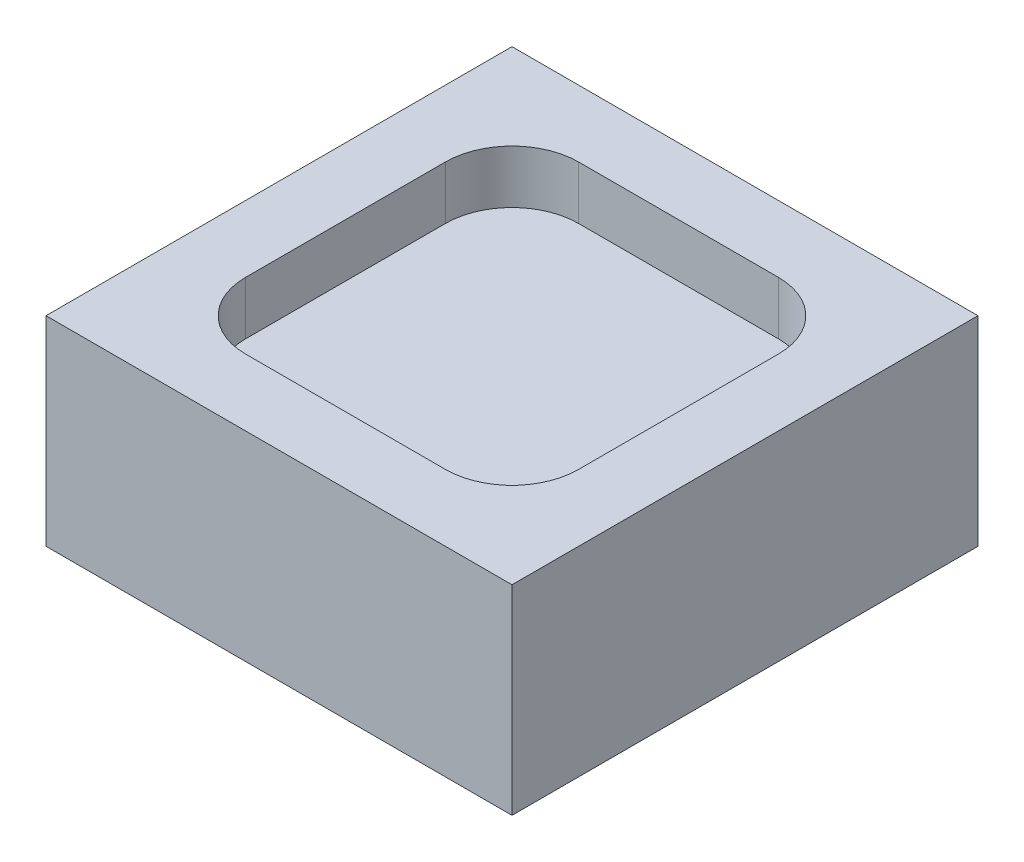
SolidWorks part; units mm, degrees
ref_plane "Front Plane" through (0, 0, 0) normal (0, 0, 1) x (1, 0, 0)
ref_plane "Top Plane" through (0, 0, 0) normal (0, 1, 0) x (1, 0, 0)
ref_plane "Right Plane" through (0, 0, 0) normal (1, 0, 0) x (0, 0, -1)
sketch "Sketch1" plane through (0, 0, 0) normal (0, 1, 0) x (1, 0, 0)
  line L1 (-3.5, 3.5) -> (3.5, 3.5)
  line L2 (-3.5, 3.5) -> (-3.5, -3.5)
  line L3 (-3.5, -3.5) -> (3.5, -3.5)
  line L4 (3.5, 3.5) -> (3.5, -3.5)
  line L5 (-3.5, 3.5) -> (3.5, -3.5) construction
  line L6 (-3.5, -3.5) -> (3.5, 3.5) construction
  point P0 (0, 0)
  point P6 (0, 0)
  dimension "D1" = 7
extrude "Boss-Extrude1" add sketch "Sketch1" along normal blind 3
sketch "Sketch2" plane through (0, 3, 0) normal (0, 1, 0) x (1, 0, 0)
  line L1 (-1.5, 2.5) -> (1.5, 2.5)
  line L2 (-2.5, 1.5) -> (-2.5, -1.5)
  line L3 (-1.5, -2.5) -> (1.5, -2.5)
  line L4 (2.5, 1.5) -> (2.5, -1.5)
  line L5 (-2.5, 2.5) -> (2.5, -2.5) construction
  line L6 (-2.5, -2.5) -> (2.5, 2.5) construction
  arc A0 (-2.5, -1.5) -> (-1.5, -2.5) centre (-1.5, -1.5) ccw
  arc A1 (1.5, -2.5) -> (2.5, -1.5) centre (1.5, -1.5) ccw
  arc A2 (1.5, 2.5) -> (2.5, 1.5) centre (1.5, 1.5) cw
  arc A3 (-1.5, 2.5) -> (-2.5, 1.5) centre (-1.5, 1.5) ccw
  point P0 (0, 0)
  dimension "D2" = 1
  dimension "D1" = 5
extrude "Cut-Extrude1" cut sketch "Sketch2" against normal blind 0.8
